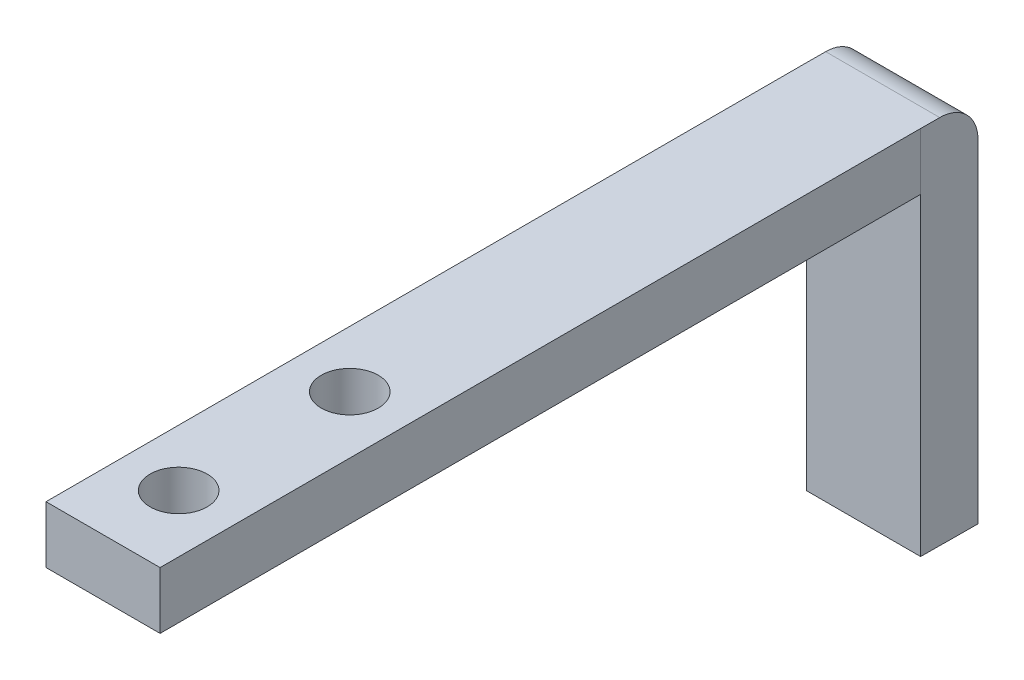
SolidWorks part; units mm, degrees
ref_plane "Front Plane" through (0, 0, 0) normal (0, 0, 1) x (1, 0, 0)
ref_plane "Top Plane" through (0, 0, 0) normal (0, 1, 0) x (1, 0, 0)
ref_plane "Right Plane" through (0, 0, 0) normal (1, 0, 0) x (0, 0, -1)
sketch "Sketch3" plane through (0, -9.5, 0) normal (0, -1, 0) x (1, 0, 0)
  line L0 (20.5409, -1) -> (26.541, -1)
  line L1 (20.5409, -1) -> (20.5237, 2)
  line L2 (26.541, -1) -> (26.5238, 2)
  line L3 (20.5237, 2) -> (26.5238, 2)
  dimension "D1" = 3
  dimension "D2" = 6
extrude "Boss-Extrude1" add sketch "Sketch3" against normal blind 19.5
sketch "Sketch5" plane through (0, 0, 2) normal (0, 0, 1) x (1, 0, 0)
  line L0 (26.5238, 10) -> (20.5237, 10)
  line L1 (26.5238, 10) -> (26.5238, 7)
  line L2 (20.5237, 10) -> (20.5237, 7)
  line L3 (26.5238, 7) -> (20.5237, 7)
  line L6 (26.5238, 10) -> (26.5238, -9.5) construction
  line L7 (20.5237, 10) -> (20.5237, -9.5) construction
  line L8 (26.5238, 10) -> (20.5237, 10) construction
  point P0 (26.5238, -47.0876)
  dimension "D1" = 3
extrude "Boss-Extrude2" add sketch "Sketch5" along normal blind 40
fillet "Fillet1" radius 2 1 edges at (23.5409, 10, -1)
sketch "Sketch6" plane through (0, 7, 0) normal (0, -1, 0) x (1, 0, 0)
  line L0 (20.5237, 42) -> (26.5238, 42) construction
  line L1 (23.5, 38) -> (23.5, 29) construction
  line L3 (20.5237, 42) -> (20.5237, 2) construction
  circle A0 centre (23.5, 38) radius 1.5
  circle A1 centre (23.5, 29) radius 1.5
  point P8 (0, 0)
  dimension "D2" = 3
  dimension "D3" = 3
  dimension "D1" = 4
  dimension "D4" = 9
extrude "Cut-Extrude1" cut sketch "Sketch6" against normal through all
